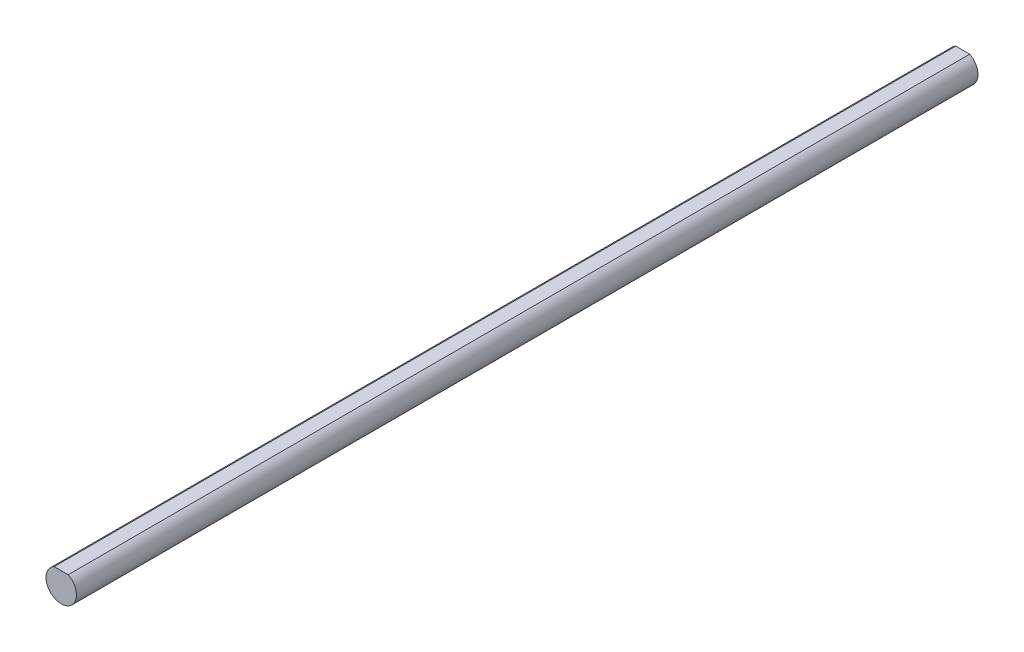
SolidWorks part; units mm, degrees
material "Alloy Steel"
ref_plane "Front Plane" through (0, 0, 0) normal (0, 0, 1) x (1, 0, 0)
ref_plane "Top Plane" through (0, 0, 0) normal (0, 1, 0) x (1, 0, 0)
ref_plane "Right Plane" through (0, 0, 0) normal (1, 0, 0) x (0, 0, -1)
sketch "Sketch1" plane through (0, 0, 0) normal (0, 0, 1) x (1, 0, 0)
  line L0 (-1.0878, 2.1) -> (1.0878, 2.1)
  arc A0 (-1.0878, 2.1) -> (1.0878, 2.1) centre (0, 0) ccw
  dimension "D1" = 4.73
  dimension "D2" = 2.1
extrude "Extrude1" add sketch "Sketch1" against normal mid plane 140
